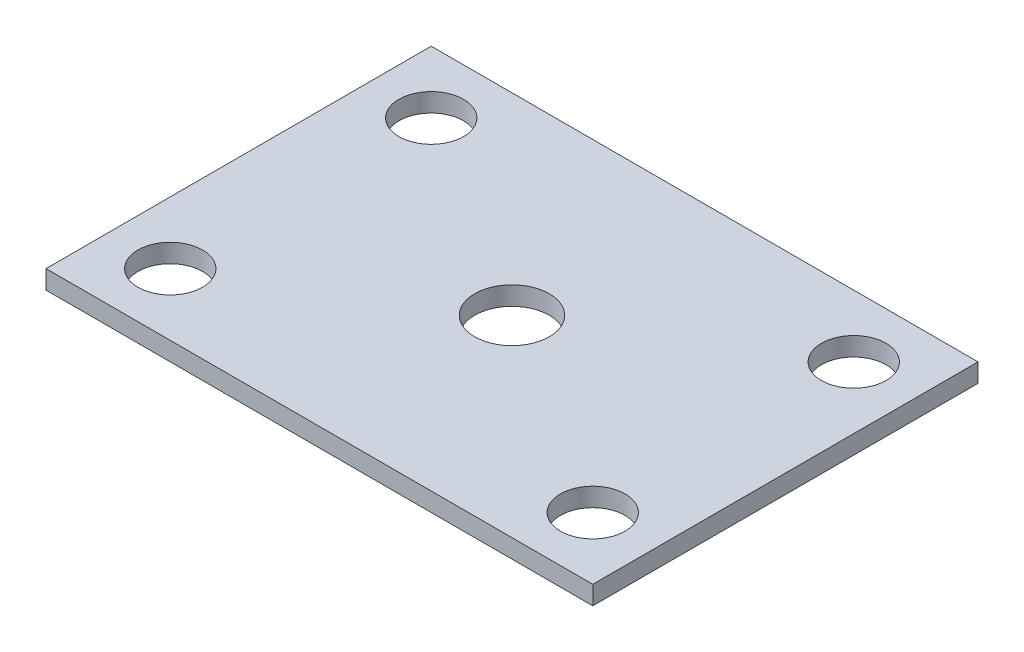
SolidWorks part; units mm, degrees
ref_plane "Front Plane" through (0, 0, 0) normal (0, 0, 1) x (1, 0, 0)
ref_plane "Top Plane" through (0, 0, 0) normal (0, 1, 0) x (1, 0, 0)
ref_plane "Right Plane" through (0, 0, 0) normal (1, 0, 0) x (0, 0, -1)
sketch "Sketch1" plane through (0, 0, 0) normal (0, 1, 0) x (1, 0, 0)
  line L1 (22, -15.5) -> (-22, -15.5)
  line L2 (22, -15.5) -> (22, 15.5)
  line L3 (22, 15.5) -> (-22, 15.5)
  line L4 (-22, -15.5) -> (-22, 15.5)
  line L5 (22, -15.5) -> (-22, 15.5) construction
  line L6 (22, 15.5) -> (-22, -15.5) construction
  point P0 (0, 0)
extrude "Boss-Extrude1" add sketch "Sketch1" along normal blind 1.5
sketch "Sketch2" plane through (0, 1.5, 0) normal (0, 1, 0) x (1, 0, 0)
  line L0 (-12.0327, 0) -> (16.3343, 0) construction
  line L1 (0, 10.5795) -> (0, -4.941) construction
  line L2 (-22, 15.5) -> (-22, -15.5) construction
  line L3 (22, 15.5) -> (-22, 15.5) construction
  circle A0 centre (-17, 10.5) radius 2.6
  circle A1 centre (17, 10.5) radius 2.6
  circle A2 centre (17, -10.5) radius 2.6
  circle A3 centre (-17, -10.5) radius 2.6
  circle A4 centre (0, 0) radius 3
  dimension "D1" = 5
  dimension "D2" = 5
extrude "Cut-Extrude1" cut sketch "Sketch2" against normal blind 1.5
